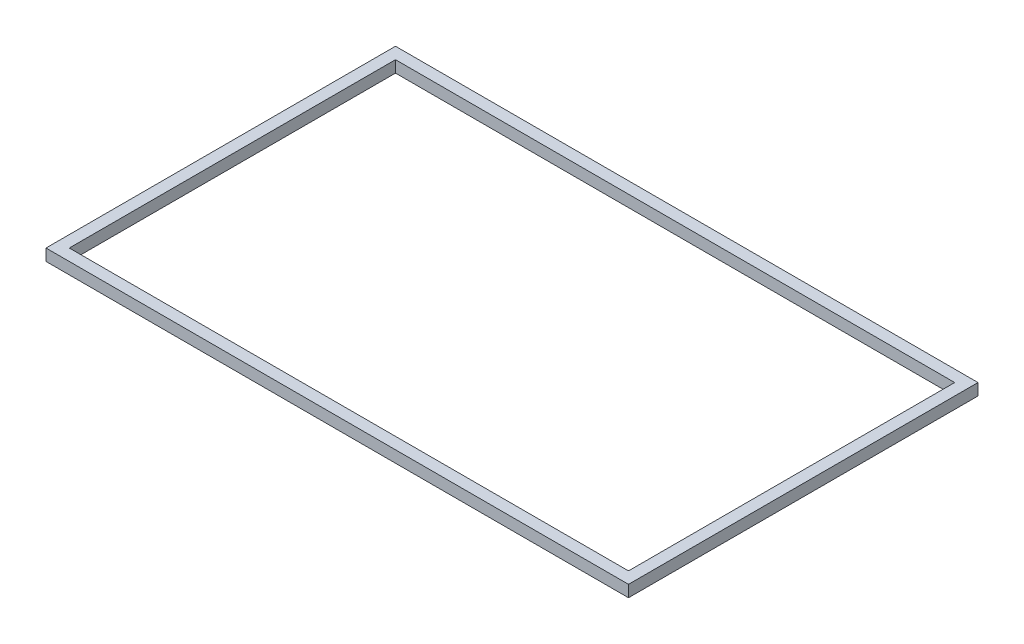
SolidWorks part; units mm, degrees
ref_plane "Front Plane" through (0, 0, 0) normal (0, 0, 1) x (1, 0, 0)
ref_plane "Top Plane" through (0, 0, 0) normal (0, 1, 0) x (1, 0, 0)
ref_plane "Right Plane" through (0, 0, 0) normal (1, 0, 0) x (0, 0, -1)
sketch "Sketch1" plane through (0, 0, 0) normal (0, 1, 0) x (1, 0, 0)
  line L1 (0, 0) -> (250, 0)
  line L2 (0, 0) -> (0, 150)
  line L3 (0, 150) -> (250, 150)
  line L4 (250, 0) -> (250, 150)
extrude "Boss-Extrude1" add sketch "Sketch1" along normal blind 5
sketch "Sketch2" plane through (0, 5, 0) normal (0, 1, 0) x (1, 0, 0)
  line L0 (250, 0) -> (250, 150) construction
  line L1 (5, 5) -> (245, 5)
  line L2 (5, 5) -> (5, 145)
  line L3 (5, 145) -> (245, 145)
  line L4 (245, 5) -> (245, 68.5227)
  line L6 (235, 81.4773) -> (245, 81.4773)
  line L8 (235, 81.4773) -> (235, 68.5227)
  line L10 (235, 68.5227) -> (245, 68.5227)
  line L12 (245, 81.4773) -> (245, 145)
  line L13 (235, 81.4773) -> (250, 71.7614) construction
  line L14 (235, 68.5227) -> (245, 75) construction
  point P4 (245, 75)
extrude "Cut-Extrude1" cut sketch "Sketch2" against normal blind 5
hole_wizard "CSK for #8 Flat Head Machine Screw (100)1" positions "3DSketch1" profile "Sketch3" countersink size "#8" standard "ANSI Inch" end condition through all
sketch3d "3DSketch1"
  point P0 (240.1109, 5, -75.136)
  point P3 (240.1109, 5, -75.136)
sketch "Sketch3" plane through (240.1109, 5, -75.136) normal (1, 0, 0) x (0, 0, 1)
  line L0 (0, 0) -> (0, 5)
  line L1 (0, 5) -> (2.2479, 5)
  line L2 (2.2479, 5) -> (2.2479, 1.6518)
  line L3 (2.2479, 1.6518) -> (4.2164, 0)
  line L5 (4.2164, 0) -> (0, 0)
  line L6 (-2.2479, 1.6518) -> (-4.2164, 0) construction
  line L11 (0, -6.35) -> (0, 107.95) construction
  dimension "Thru Hole Dia." = 4.4958
  dimension "Thru Hole Depth" = 5
  dimension "Near C'Sink Dia." = 8.4328
  dimension "Near C'Sink Angle" = 100
sketch "Sketch4" plane through (0, 5, 0) normal (0, 1, 0) x (1, 0, 0)
  line L1 (245, 81.4773) -> (235, 81.4773)
  line L2 (245, 81.4773) -> (245, 68.5227)
  line L3 (245, 68.5227) -> (235, 68.5227)
  line L4 (235, 81.4773) -> (235, 68.5227)
extrude "Cut-Extrude2" cut sketch "Sketch4" against normal blind 10
